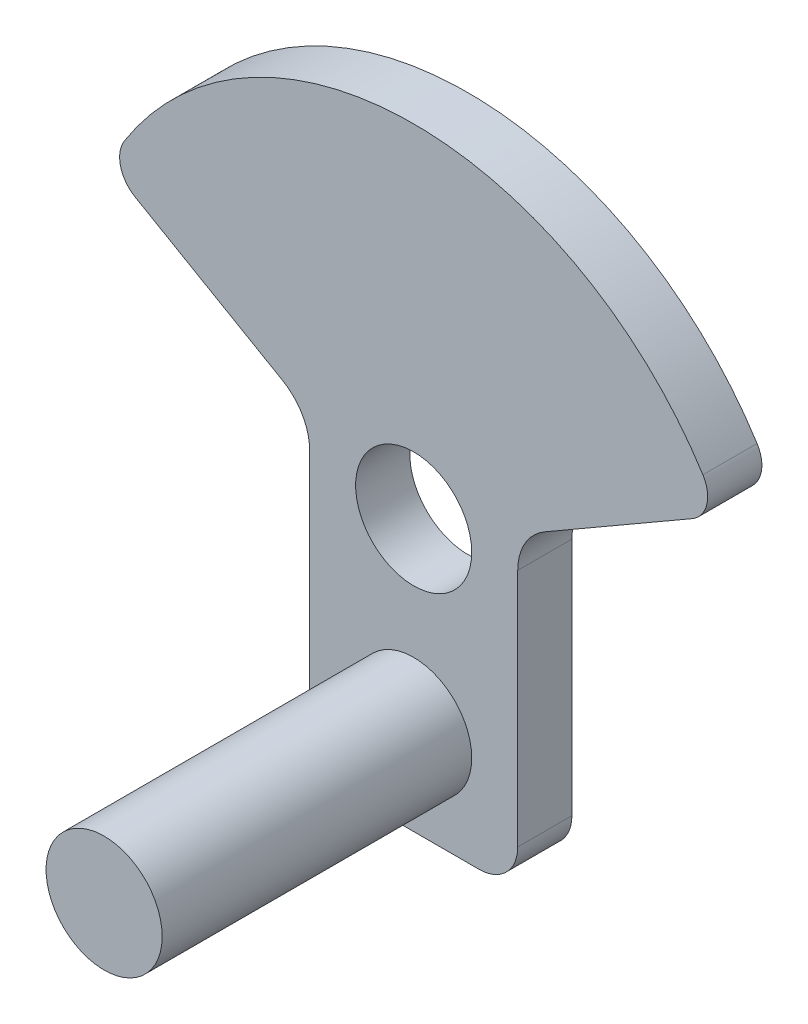
SolidWorks part; units mm, degrees
material "AISI 1020"
ref_plane "Front Plane" through (0, 0, 0) normal (0, 0, 1) x (1, 0, 0)
ref_plane "Top Plane" through (0, 0, 0) normal (0, 1, 0) x (1, 0, 0)
ref_plane "Right Plane" through (0, 0, 0) normal (1, 0, 0) x (0, 0, -1)
sketch "Sketch2" plane through (0, 0, 0) normal (0, 0, 1) x (1, 0, 0)
  line L0 (5, 0) -> (21.8951, 0)
  line L1 (26.8951, 5) -> (26.8951, 35.9585)
  line L2 (30.3951, 42.0207) -> (49.4401, 53.0164)
  line L3 (0, 5) -> (0, 35.9585)
  line L4 (-3.5, 42.0207) -> (-22.545, 53.0164)
  circle A1 centre (13.4476, 35) radius 7.5
  arc A2 (-23.9265, 58.6173) -> (50.8216, 58.6173) centre (13.4476, 35) cw
  arc A3 (21.8951, 0) -> (26.8951, 5) centre (21.8951, 5) ccw
  arc A4 (5, 0) -> (0, 5) centre (5, 5) cw
  arc A5 (30.3951, 42.0207) -> (26.8951, 35.9585) centre (33.8951, 35.9585) ccw
  arc A6 (0, 35.9585) -> (-3.5, 42.0207) centre (-7, 35.9585) ccw
  arc A7 (-23.9265, 58.6173) -> (-22.545, 53.0164) centre (-20.545, 56.4805) ccw
  arc A8 (50.8216, 58.6173) -> (49.4401, 53.0164) centre (47.4401, 56.4805) cw
  point P13 (26.8951, 0)
  point P16 (0, 0)
  point P19 (26.8951, 40)
  point P22 (0, 40)
  point P25 (-25.9808, 55)
  point P28 (52.8759, 55)
  dimension "D2" = 30
  dimension "D8" = 44.2108
  dimension "D9" = 5
  dimension "D10" = 7
  dimension "D11" = 4
  dimension "D1" = 30
  dimension "D4" = 120
  dimension "D5" = 40
  dimension "D6" = 40
  dimension "D7" = 35
extrude "Boss-Extrude5" add sketch "Sketch2" along normal blind 7 contours L2 A8 A2 A7 L4 A6 L3 A4 L0 A3 L1 A5 | A1
sketch "Sketch3" plane through (0, 0, 7) normal (0, 0, 1) x (1, 0, 0)
  line L0 (5, 0) -> (21.8951, 0) construction
  circle A0 centre (13.4476, 12) radius 7.5
  circle A1 centre (13.4476, 35) radius 7.5 construction
  dimension "D1" = 12
extrude "Boss-Extrude6" add sketch "Sketch3" along normal blind 40 contours A0
